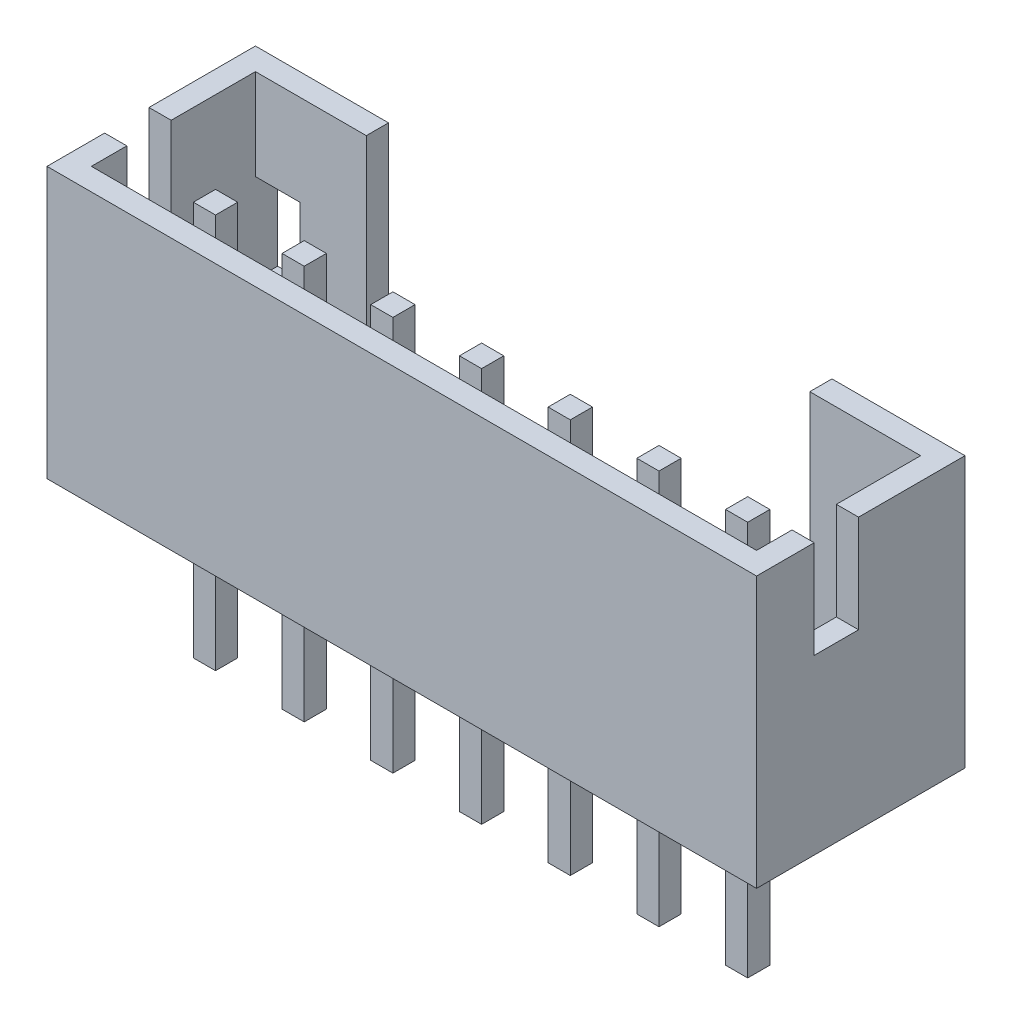
SolidWorks part; units mm, degrees
ref_plane "Front Plane" through (0, 0, 0) normal (0, 0, 1) x (1, 0, 0)
ref_plane "Top Plane" through (0, 0, 0) normal (0, 1, 0) x (1, 0, 0)
ref_plane "Right Plane" through (0, 0, 0) normal (1, 0, 0) x (0, 0, -1)
sketch "Sketch1" plane through (0, 0, 0) normal (0, 1, 0) x (1, 0, 0)
  line L1 (-8, -2.35) -> (8, -2.35)
  line L2 (-8, -2.35) -> (-8, 2.35)
  line L3 (-8, 2.35) -> (8, 2.35)
  line L4 (8, -2.35) -> (8, 2.35)
  line L5 (-8, -2.35) -> (8, 2.35) construction
  line L6 (-8, 2.35) -> (8, -2.35) construction
  point P0 (0, 0)
  dimension "D1" = 4.7
  dimension "D2" = 16
extrude "casing" add sketch "Sketch1" along normal blind 6.1
shell "casing_shell" thickness 0.5
sketch "Sketch2" plane through (0, 0.5, 0) normal (0, 1, 0) x (1, 0, 0)
  line L0 (-7.5, -0.55) -> (7.5, -0.55) construction
  line L1 (-7.5, 1.85) -> (-7.5, -1.85) construction
  line L2 (7.5, -1.85) -> (7.5, 1.85) construction
  line L3 (-8, -2.35) -> (8, -2.35) construction
  line L5 (-6.25, -0.3) -> (-5.75, -0.3)
  line L6 (-6.25, -0.3) -> (-6.25, -0.8)
  line L7 (-6.25, -0.8) -> (-5.75, -0.8)
  line L8 (-5.75, -0.3) -> (-5.75, -0.8)
  line L9 (-6.25, -0.3) -> (-5.75, -0.8) construction
  line L10 (-6.25, -0.8) -> (-5.75, -0.3) construction
  line L11 (-4.25, -0.3) -> (-4.25, -0.8)
  line L12 (-4.25, -0.3) -> (-3.75, -0.3)
  line L13 (-3.75, -0.3) -> (-3.75, -0.8)
  line L14 (-4.25, -0.8) -> (-3.75, -0.8)
  line L15 (-2.25, -0.3) -> (-2.25, -0.8)
  line L16 (-2.25, -0.3) -> (-1.75, -0.3)
  line L17 (-1.75, -0.3) -> (-1.75, -0.8)
  line L18 (-2.25, -0.8) -> (-1.75, -0.8)
  line L19 (-0.25, -0.3) -> (-0.25, -0.8)
  line L20 (-0.25, -0.3) -> (0.25, -0.3)
  line L21 (0.25, -0.3) -> (0.25, -0.8)
  line L22 (-0.25, -0.8) -> (0.25, -0.8)
  line L23 (1.75, -0.3) -> (1.75, -0.8)
  line L24 (1.75, -0.3) -> (2.25, -0.3)
  line L25 (2.25, -0.3) -> (2.25, -0.8)
  line L26 (1.75, -0.8) -> (2.25, -0.8)
  line L27 (3.75, -0.3) -> (3.75, -0.8)
  line L28 (3.75, -0.3) -> (4.25, -0.3)
  line L29 (4.25, -0.3) -> (4.25, -0.8)
  line L30 (3.75, -0.8) -> (4.25, -0.8)
  line L31 (5.75, -0.3) -> (5.75, -0.8)
  line L32 (5.75, -0.3) -> (6.25, -0.3)
  line L33 (6.25, -0.3) -> (6.25, -0.8)
  line L34 (5.75, -0.8) -> (6.25, -0.8)
  line L35 (-6.25, -0.3) -> (-4.25, -0.3) construction
  point P8 (-6, -0.55)
  point P13 (0, -0.3)
  dimension "D1" = 1.8
  dimension "D2" = 0.5
  dimension "D5" = 2
  dimension "D4" = 7
extrude "pins" add sketch "Sketch2" along normal blind 5 and the other way blind 3.9 separate body
sketch "Sketch3" plane through (0, 0, -2.35) normal (0, 0, -1) x (-1, 0, 0)
  line L0 (-8, 6.1) -> (8, 6.1) construction
  line L1 (-5, 6.1) -> (5, 6.1)
  line L2 (-5, 6.1) -> (-5, 1.5)
  line L3 (-5, 1.5) -> (5, 1.5)
  line L4 (5, 6.1) -> (5, 1.5)
  line L5 (-5.75, -3.4) -> (-5.75, 5.5) construction
  line L7 (-8, 0) -> (8, 0) construction
  line L8 (-8, 6.1) -> (-8, 0) construction
  line L9 (-6.5, 2.05) -> (-7.5, 2.05)
  line L10 (-6.5, 2.05) -> (-6.5, 4.05)
  line L11 (-6.5, 4.05) -> (-7.5, 4.05)
  line L12 (-7.5, 2.05) -> (-7.5, 4.05)
  line L13 (-6.5, 2.05) -> (-7.5, 4.05) construction
  line L14 (-6.5, 4.05) -> (-7.5, 2.05) construction
  line L15 (0, 2.585) -> (0, -2.585) construction
  line L16 (6.5, 4.05) -> (7.5, 4.05)
  line L17 (7.5, 2.05) -> (7.5, 4.05)
  line L18 (6.5, 2.05) -> (7.5, 2.05)
  line L19 (6.5, 2.05) -> (6.5, 4.05)
  point P10 (-7, 3.05)
  point P15 (0, 0)
  point P18 (-8, 3.05)
  point P20 (0, 0)
  dimension "D1" = 0.75
  dimension "D2" = 10
  dimension "D3" = 1.5
  dimension "D4" = 1
  dimension "D5" = 2
  dimension "D6" = 0.5
extrude "shape_cut1" cut sketch "Sketch3" against normal up to surface (0.5 mm away) up to face at (0, 3.3, -1.85)
sketch "Sketch4" plane through (-8, 0, 0) normal (-1, 0, 0) x (0, 0, 1)
  line L0 (-2.35, 6.1) -> (2.35, 6.1) construction
  line L1 (1.05, 3.9) -> (0.05, 3.9)
  line L2 (1.05, 3.9) -> (1.05, 6.1)
  line L3 (1.05, 6.1) -> (0.05, 6.1)
  line L4 (0.05, 3.9) -> (0.05, 6.1)
  line L5 (1.05, 3.9) -> (0.05, 6.1) construction
  line L6 (1.05, 6.1) -> (0.05, 3.9) construction
  line L7 (-2.35, 0) -> (2.35, 0) construction
  line L8 (-2.35, 6.1) -> (-2.35, 0) construction
  point P0 (0.55, 5)
  dimension "D1" = 5
  dimension "D2" = 1
  dimension "D3" = 2.4
extrude "shape_cut2" cut sketch "Sketch4" against normal up to surface (15.5 mm away)
mirror "shape_cut2m" about plane through (0, 0, 0) normal (1, 0, 0) of "shape_cut2"
